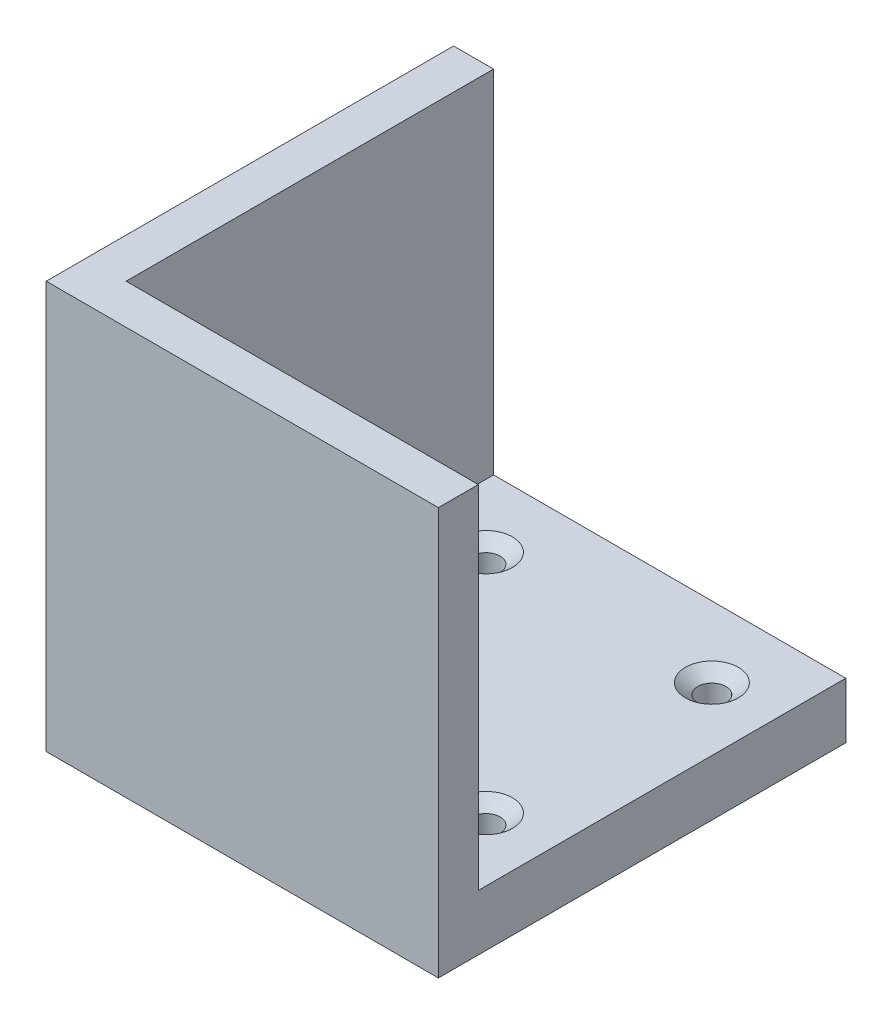
SolidWorks part; units mm, degrees
material "6061-T6 (SS)"
ref_plane "Front Plane" through (0, 0, 0) normal (0, 0, 1) x (1, 0, 0)
ref_plane "Top Plane" through (0, 0, 0) normal (0, 1, 0) x (1, 0, 0)
ref_plane "Right Plane" through (0, 0, 0) normal (1, 0, 0) x (0, 0, -1)
sketch "MotorProfile" plane through (0, 0, 0) normal (0, 1, 0) x (1, 0, 0)
  line L1 (-28, -29.21) -> (28, -29.21)
  line L2 (-28, -29.21) -> (-28, 29.21)
  line L3 (-28, 29.21) -> (28, 29.21)
  line L4 (28, -29.21) -> (28, 29.21)
  line L5 (-28, -29.21) -> (28, 29.21) construction
  line L6 (-28, 29.21) -> (28, -29.21) construction
  point P0 (0, 0)
  dimension "D1" = 56
  dimension "D2" = 58.42
sketch "Sketch2" plane through (0, 0, 0) normal (0, 1, 0) x (1, 0, 0)
  line L0 (-34.35, 29.21) -> (-34.35, -35.56)
  line L5 (-34.35, -35.56) -> (28, -35.56)
  line L6 (-28, -29.21) -> (-28, 29.21) construction
  line L7 (-34.35, 29.21) -> (-28, 29.21)
  line L8 (-28, 29.21) -> (-28, -29.21)
  line L9 (-28, -29.21) -> (28, -29.21)
  line L13 (28, -29.21) -> (28, -35.56)
  dimension "D1" = 6.35
  dimension "D2" = 6.35
  dimension "D3" = 28
  dimension "D4" = 29.21
sketch "Sketch3" plane through (0, 0, 0) normal (0, 1, 0) x (1, 0, 0)
  line L0 (17.9605, -17.9605) -> (-17.9605, 17.9605)
  line L1 (-17.9605, 17.9605) -> (-17.9605, -45.5395)
  line L2 (-17.9605, -45.5395) -> (53.8815, -45.5395)
  line L3 (17.9605, -17.9605) -> (53.8815, 17.9605)
  line L4 (53.8815, 17.9605) -> (53.8815, -45.5395)
  line L5 (0, 0) -> (104.1503, 0) construction
  point P4 (0, 0)
  dimension "D1" = 50.8
  dimension "D2" = 50.8
  dimension "D3" = 63.5
  dimension "D4" = 45
  dimension "D5" = 45
extrude "Boss-Extrude1" [suppressed] add sketch "Sketch3" along normal blind 50.8
extrude "Boss-Extrude2" add sketch "MotorProfile" along normal blind 8.89
extrude "Boss-Extrude3" add sketch "Sketch2" along normal blind 64.77
sketch "Sketch4" plane through (28, 0, 0) normal (1, 0, 0) x (0, 0, -1)
  line L1 (-35.56, 0) -> (29.21, 0)
  line L2 (-35.56, 0) -> (-35.56, 8.89)
  line L3 (-35.56, 8.89) -> (29.21, 8.89)
  line L4 (29.21, 0) -> (29.21, 8.89)
sketch "Sketch10" plane through (28, 0, 0) normal (1, 0, 0) x (0, 0, -1)
  line L0 (-29.21, 8.89) -> (-29.21, 0)
  line L1 (-29.21, 0) -> (29.21, 0)
  line L3 (-29.21, 8.89) -> (29.21, 8.89)
  line L4 (29.21, 0) -> (29.21, 8.89)
sketch "Sketch7" plane through (0, 8.89, 0) normal (0, 1, 0) x (1, 0, 0)
  line L0 (-17.9605, 17.9605) -> (-17.9605, -17.9605) construction
  line L1 (-17.9605, 17.9605) -> (17.9605, 17.9605) construction
  point P1 (-17.9605, 17.9605)
  point P2 (17.9605, 17.9605)
  point P3 (-17.9605, -17.9605)
  point P4 (17.9605, -17.9605)
  point P7 (0, 17.9605)
  point P9 (-17.9605, 0)
  dimension "D1" = 35.921
  dimension "D2" = 35.921
hole_wizard "CSK for #8 Flat Head Machine Screw (100)2" positions "Sketch8" profile "Sketch9" countersink size "#8" standard "ANSI Inch" end condition through all
sketch "Sketch8" plane through (0, 8.89, 0) normal (0, 1, 0) x (1, 0, 0)
  point P0 (17.9605, 17.9605)
  point P3 (17.9605, -17.9605)
  point P6 (-17.9605, -17.9605)
  point P9 (-17.9605, 17.9605)
  point P12 (-17.9605, -17.9605)
  point P14 (-17.9605, 17.9605)
  point P16 (17.9605, -17.9605)
  point P18 (17.9605, 17.9605)
sketch "Sketch9" plane through (17.9605, 8.89, -17.9605) normal (1, 0, 0) x (0, 0, 1)
  line L0 (0, 0) -> (0, 8.89)
  line L1 (0, 8.89) -> (2.2479, 8.89)
  line L2 (2.2479, 8.89) -> (2.2479, 1.6518)
  line L3 (2.2479, 1.6518) -> (4.2164, 0)
  line L5 (4.2164, 0) -> (0, 0)
  line L6 (-2.2479, 1.6518) -> (-4.2164, 0) construction
  line L11 (0, -6.35) -> (0, 107.95) construction
  dimension "Thru Hole Dia." = 4.4958
  dimension "Thru Hole Depth" = 8.89
  dimension "Near C'Sink Dia." = 8.4328
  dimension "Near C'Sink Angle" = 100
equation "\"1n\"=0.5"
